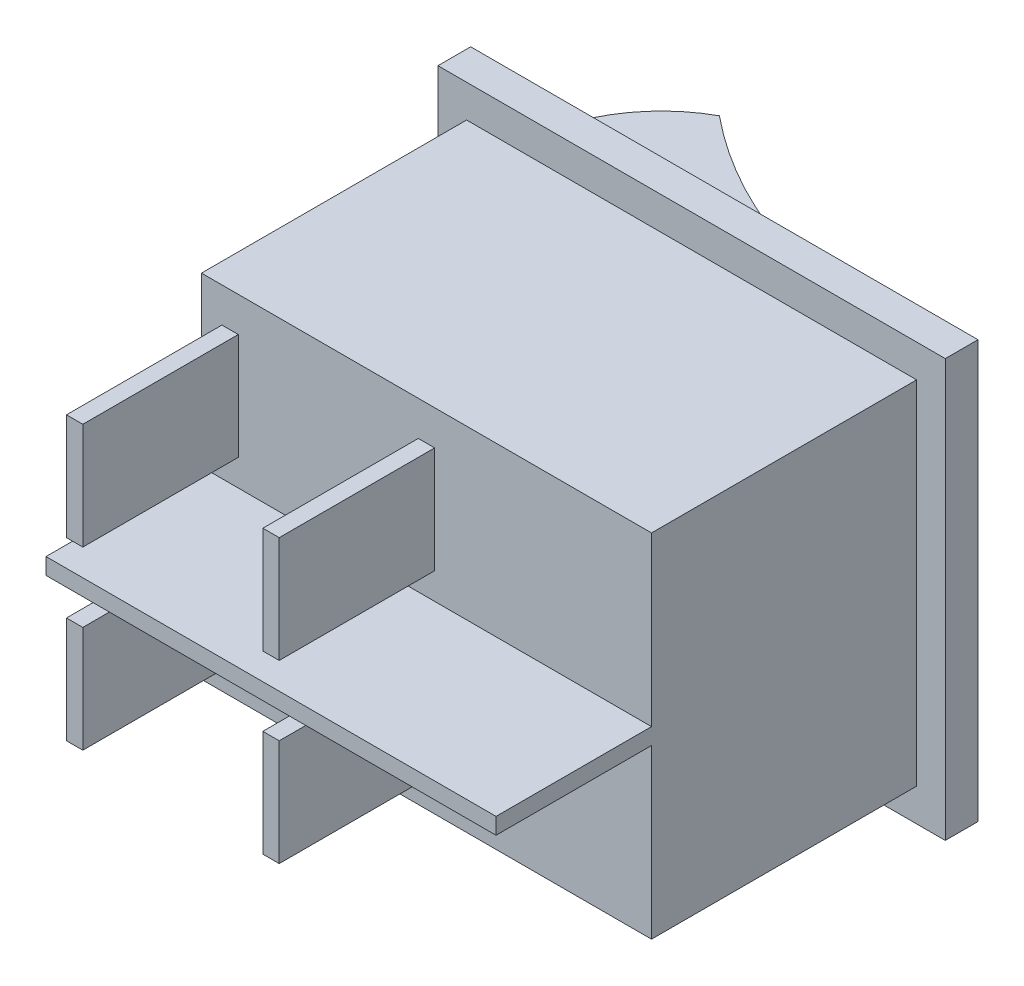
SolidWorks part; units mm, degrees
ref_plane "Plano frontal" through (0, 0, 0) normal (0, 0, 1) x (1, 0, 0)
ref_plane "Plano superior" through (0, 0, 0) normal (0, 1, 0) x (1, 0, 0)
ref_plane "Plano direito" through (0, 0, 0) normal (1, 0, 0) x (0, 0, -1)
sketch "Esboço1" plane through (0, 0, 0) normal (0, 0, 1) x (1, 0, 0)
  line L1 (15.5, -12.75) -> (-15.5, -12.75)
  line L2 (15.5, -12.75) -> (15.5, 12.75)
  line L3 (15.5, 12.75) -> (-15.5, 12.75)
  line L4 (-15.5, -12.75) -> (-15.5, 12.75)
  line L5 (15.5, -12.75) -> (-15.5, 12.75) construction
  line L6 (15.5, 12.75) -> (-15.5, -12.75) construction
  point P0 (0, 0)
  dimension "D1" = 31
  dimension "D2" = 25.5
extrude "Ressalto-extrusão1" add sketch "Esboço1" along normal blind 2
sketch "Esboço2" plane through (0, 0, 2) normal (0, 0, 1) x (1, 0, 0)
  line L1 (13.75, -10.75) -> (-13.75, -10.75)
  line L2 (13.75, -10.75) -> (13.75, 10.75)
  line L3 (13.75, 10.75) -> (-13.75, 10.75)
  line L4 (-13.75, -10.75) -> (-13.75, 10.75)
  line L5 (13.75, -10.75) -> (-13.75, 10.75) construction
  line L6 (13.75, 10.75) -> (-13.75, -10.75) construction
  point P0 (0, 0)
  dimension "D1" = 27.5
  dimension "D2" = 21.5
extrude "Ressalto-extrusão2" add sketch "Esboço2" along normal blind 16.2
sketch "Esboço3" plane through (0, 0, 18.2) normal (0, 0, 1) x (1, 0, 0)
  line L0 (-20.0293, 0) -> (20.5648, 0) construction
  line L1 (0, -14.8613) -> (0, 15.9699) construction
  line L2 (-13.75, 10.75) -> (-13.75, -10.75) construction
  line L3 (-11.5, 2.125) -> (-12.5, 2.125)
  line L4 (-11.5, 2.125) -> (-11.5, 8.625)
  line L5 (-11.5, 8.625) -> (-12.5, 8.625)
  line L6 (-12.5, 2.125) -> (-12.5, 8.625)
  line L7 (-11.5, 2.125) -> (-12.5, 8.625) construction
  line L8 (-11.5, 8.625) -> (-12.5, 2.125) construction
  line L9 (0.5, -2.125) -> (-0.5, -2.125)
  line L10 (0.5, 2.125) -> (-0.5, 2.125)
  line L11 (0.5, 2.125) -> (0.5, 8.625)
  line L12 (0.5, 8.625) -> (-0.5, 8.625)
  line L13 (-0.5, 2.125) -> (-0.5, 8.625)
  line L14 (0.5, 2.125) -> (-0.5, 8.625) construction
  line L15 (0.5, 8.625) -> (-0.5, 2.125) construction
  line L16 (0.5, -2.125) -> (0.5, -8.625)
  line L17 (0.5, -8.625) -> (-0.5, -8.625)
  line L18 (-0.5, -2.125) -> (-0.5, -8.625)
  line L19 (-11.5, -2.125) -> (-12.5, -2.125)
  line L20 (-12.5, -2.125) -> (-12.5, -8.625)
  line L21 (-11.5, -8.625) -> (-12.5, -8.625)
  line L22 (-11.5, -2.125) -> (-11.5, -8.625)
  line L23 (-13.75, 10.75) -> (-13.75, -10.75) construction
  line L24 (13.75, -0.5) -> (-13.75, -0.5)
  line L25 (13.75, -0.5) -> (13.75, 0.5)
  line L26 (13.75, 0.5) -> (-13.75, 0.5)
  line L27 (-13.75, -0.5) -> (-13.75, 0.5)
  line L28 (13.75, -0.5) -> (-13.75, 0.5) construction
  line L29 (13.75, 0.5) -> (-13.75, -0.5) construction
  point P5 (-12, 5.375)
  point P12 (0, 5.375)
  point P25 (0, 0)
  dimension "D1" = 6.5
  dimension "D2" = 1
  dimension "D3" = 1.25
  dimension "D4" = 5.375
  dimension "D5" = 1
extrude "Ressalto-extrusão3" add sketch "Esboço3" along normal blind 9.5
sketch "Esboço4" plane through (0, 0, 0) normal (0, 0, -1) x (-1, 0, 0)
  line L1 (12, -9.5) -> (-12, -9.5)
  line L2 (12, -9.5) -> (12, 9.5)
  line L3 (12, 9.5) -> (-12, 9.5)
  line L4 (-12, -9.5) -> (-12, 9.5)
  line L5 (12, -9.5) -> (-12, 9.5) construction
  line L6 (12, 9.5) -> (-12, -9.5) construction
  point P0 (0, 0)
  dimension "D1" = 24
  dimension "D2" = 19
extrude "Ressalto-extrusão4" add sketch "Esboço4" along normal blind 1
sketch "Esboço5" plane through (0, -9.5, 0) normal (0, -1, 0) x (1, 0, 0)
  line L0 (0, 8.0807) -> (0, -10.8576) construction
  line L1 (12, -1) -> (-12, -1) construction
  line L2 (-12, -1) -> (-12, 0) construction
  line L3 (-12, -1) -> (12, -1)
  arc A0 (-7.5, -7.2) -> (-12, -1) centre (-3.1589, 0.6838) cw
  arc A1 (-7.5, -7.2) -> (8.0246, -1) centre (10.0123, -28.5136) cw
  point P3 (-7.5, -7.2)
  point P8 (-12, -0.5)
  line M3 (-12, -1) -> (12, -1)
  dimension "D3" = 9
  dimension "D1" = 6.2
  dimension "D2" = 4.5
extrude "Ressalto-extrusão5" add sketch "Esboço5" against normal blind 19 contours L3 L0 A1 | L0 A0 A1 M3
